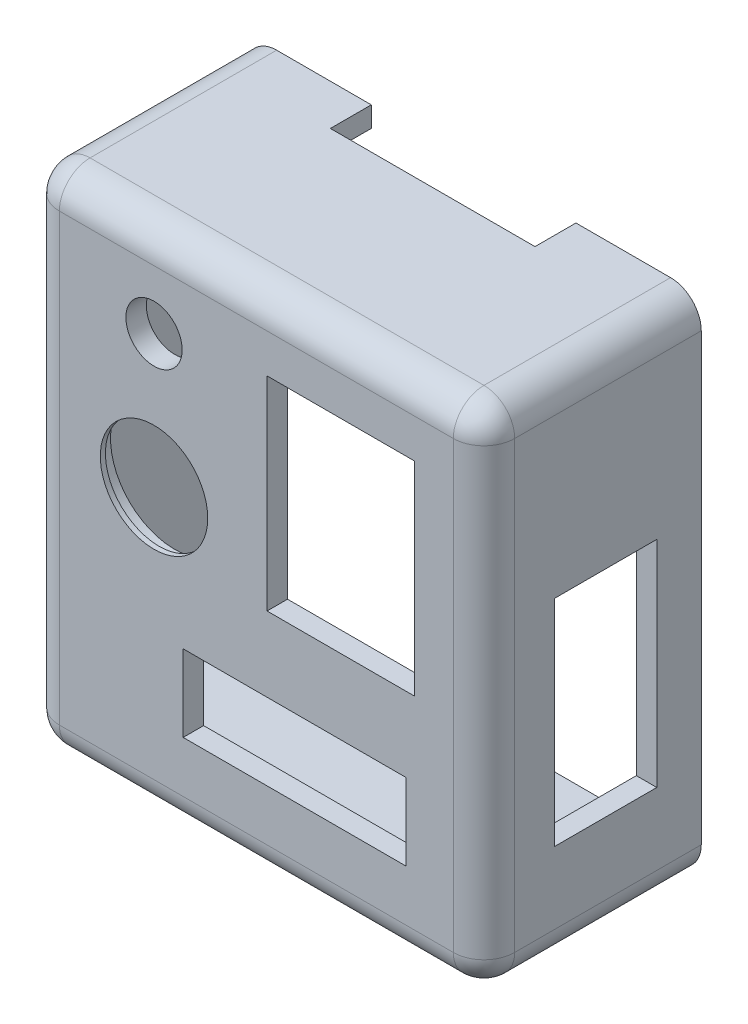
SolidWorks part; units mm, degrees
ref_plane "Front Plane" through (0, 0, 0) normal (0, 0, 1) x (1, 0, 0)
ref_plane "Top Plane" through (0, 0, 0) normal (0, 1, 0) x (1, 0, 0)
ref_plane "Right Plane" through (0, 0, 0) normal (1, 0, 0) x (0, 0, -1)
sketch "Sketch1" plane through (0, 0, 0) normal (0, 0, 1) x (1, 0, 0)
  line L1 (-64.2938, -72.2313) -> (64.2937, -72.2313)
  line L2 (-64.2938, -72.2313) -> (-64.2938, 72.2313)
  line L3 (-64.2938, 72.2313) -> (64.2937, 72.2313)
  line L4 (64.2937, -72.2313) -> (64.2937, 72.2313)
  line L5 (-64.2938, -72.2313) -> (64.2937, 72.2313) construction
  line L6 (-64.2938, 72.2313) -> (64.2937, -72.2313) construction
  point P0 (0, 0)
  dimension "D1" = 128.5875
  dimension "D2" = 144.4625
extrude "Boss-Extrude1" add sketch "Sketch1" against normal blind 61.0718 contours L3 L4 L1 L2
shell "Shell1" thickness 6.35
sketch "Sketch2" plane through (0, 0, 6.35) normal (0, 0, 1) x (1, 0, 0)
  line L0 (-70.6438, 78.5812) -> (70.6437, 78.5812) construction
  line L1 (-70.6438, -78.5812) -> (-70.6438, 78.5812) construction
  line L2 (70.6437, -78.5812) -> (70.6437, 78.5812) construction
  line L3 (3.3337, 56.9912) -> (49.0537, 56.9912)
  line L4 (3.3337, 56.9912) -> (3.3337, -6.1912)
  line L5 (3.3337, -6.1912) -> (49.0537, -6.1912)
  line L6 (49.0537, 56.9912) -> (49.0537, -6.1912)
  line L7 (3.3337, 56.9912) -> (49.0537, -6.1912) construction
  line L8 (3.3337, -6.1912) -> (49.0537, 56.9912) construction
  line L9 (-70.6438, -78.5812) -> (70.6437, -78.5812) construction
  line L10 (-22.7013, -29.3687) -> (46.5137, -29.3687)
  line L11 (-22.7013, -29.3687) -> (-22.7013, -53.1812)
  line L12 (-22.7013, -53.1812) -> (46.5137, -53.1812)
  line L13 (46.5137, -29.3687) -> (46.5137, -53.1812)
  line L14 (-22.7013, -29.3687) -> (46.5137, -53.1812) construction
  line L15 (-22.7013, -53.1812) -> (46.5137, -29.3687) construction
  circle A0 centre (-31.75, 50.8) radius 8.7312
  circle A1 centre (-31.75, 9.525) radius 19.8438
  point P8 (26.1937, 25.4)
  point P15 (11.9062, -41.275)
  dimension "D1" = 17.4625
  dimension "D4" = 39.6875
  dimension "D2" = 27.7812
  dimension "D3" = 38.8937
  dimension "D5" = 38.8937
  dimension "D6" = 69.0563
  dimension "D7" = 45.72
  dimension "D8" = 63.1825
  dimension "D9" = 21.59
  dimension "D10" = 21.59
  dimension "D11" = 69.215
  dimension "D12" = 23.8125
  dimension "D13" = 25.4
  dimension "D14" = 24.13
extrude "Cut-Extrude1" cut sketch "Sketch2" against normal through all
sketch "Sketch3" plane through (70.6437, 0, 0) normal (1, 0, 0) x (0, 0, -1)
  line L1 (15.5219, 19.9072) -> (47.2719, 19.9072)
  line L2 (15.5219, 19.9072) -> (15.5219, -46.7678)
  line L3 (15.5219, -46.7678) -> (47.2719, -46.7678)
  line L4 (47.2719, 19.9072) -> (47.2719, -46.7678)
  line L5 (15.5219, 19.9072) -> (47.2719, -46.7678) construction
  line L6 (15.5219, -46.7678) -> (47.2719, 19.9072) construction
  line L9 (61.0718, 78.5812) -> (-6.35, 78.5812) construction
  line L10 (-6.35, -78.5812) -> (-6.35, 78.5812) construction
  point P0 (31.3969, -13.4302)
  dimension "D1" = 31.75
  dimension "D2" = 66.675
  dimension "D3" = 58.674
  dimension "D4" = 21.8719
extrude "Cut-Extrude2" cut sketch "Sketch3" against normal up to surface (6.35 mm away) up to face at (64.2937, 0, -30.5359)
sketch "Sketch4" plane through (0, 0, 6.35) normal (0, 0, 1) x (1, 0, 0)
  circle A0 centre (-31.75, 9.525) radius 19.8438 construction
  circle A1 centre (-31.75, 9.525) radius 19.8438
  circle A2 centre (-31.75, 9.525) radius 16.6687
  dimension "D1" = 3.175
extrude "Boss-Extrude2" add sketch "Sketch4" against normal blind 1.5875
sketch "Sketch5" plane through (0, 78.5812, 0) normal (0, 1, 0) x (1, 0, 0)
  line L0 (-70.6438, 61.0718) -> (70.6437, 61.0718) construction
  line L1 (-31.75, 61.0718) -> (31.75, 61.0718)
  line L2 (-31.75, 61.0718) -> (-31.75, 48.3718)
  line L3 (-31.75, 48.3718) -> (31.75, 48.3718)
  line L4 (31.75, 61.0718) -> (31.75, 48.3718)
  point P6 (0, 61.0718)
  point P7 (0, 61.0718)
  dimension "D1" = 63.5
  dimension "D2" = 12.7
extrude "Cut-Extrude3" cut sketch "Sketch5" against normal up to surface (6.35 mm away) up to face at (0, 72.2313, -30.5359)
fillet "Fillet1" radius 9.525 8 edges at (70.6437, 78.5812, -27.3609) (-70.6438, 78.5812, -27.3609) (-70.6438, -78.5812, -27.3609) (70.6437, -78.5812, -27.3609) (-70.6438, 0, 6.35) (0, -78.5812, 6.35) (70.6437, 0, 6.35) (0, 78.5812, 6.35)
fillet "Fillet2" radius 3.175 8 edges at (-64.2938, -72.2313, -30.5359) (64.2937, -72.2313, -30.5359) (0, -72.2313, 0) (64.2937, 0, 0) (-64.2938, 0, 0) (-64.2938, 72.2313, -30.5359) (0, 72.2313, 0) (64.2937, 72.2313, -30.5359)
equation "\"diameter1\"= 0.6875in"
equation "\"topcircle1totop\"= 0.5 + 0.25 + ( 0.6875 / 2 )"
equation "\"leftcircle1toleft\"= 0.9375 + 0.25 + ( 0.6875 / 2 )"
equation "\"D1@Sketch2\"=\"diameter1\""
equation "\"D2@Sketch2\"=\"topcircle1totop\""
equation "\"D3@Sketch2\"=\"leftcircle1toleft\""
equation "\"diameter2\"= 1.5625in"
equation "\"topcircle2totop\"= 1.6875in + 0.25 + ( 1.5625 / 2 )"
equation "\"leftcircle2totop\"= 0.5in + 0.25 + ( 1.5625 / 2 )"
equation "\"D4@Sketch2\"=\"diameter2\""
equation "\"D5@Sketch2\"=\"leftcircle2totop\""
equation "\"D6@Sketch2\"=\"topcircle2totop\""
equation "\"boxedgetoside\"= 0.5in + 0.25 + 0.1"
equation "\"topboxtopedge\"= 1.8in"
equation "\"topboxsideedge\"= 2.4875in"
equation "\"bottomboxsideedge\"= 0.9375in"
equation "\"bottomboxtopedge\"= 2.725in"
equation "\"D7@Sketch2\"=\"topboxtopedge\""
equation "\"D8@Sketch2\"=\"topboxsideedge\""
equation "\"D9@Sketch2\"=\"boxedgetoside\""
equation "\"D10@Sketch2\"=\"boxedgetoside\""
equation "\"D11@Sketch2\"=\"bottomboxtopedge\""
equation "\"D12@Sketch2\"=\"bottomboxsideedge\""
equation "\"D13@Sketch2\"=\"bottomboxtobottomedge\""
equation "\"D14@Sketch2\"=\"bottomboxtorightedge\""
equation "\"sideboxtoleftedge\"= 0.5625 + 0.0772 / 2 + 0.26in"
equation "\"sideboxtotopedge\"= 2 + 0.25 + 0.06in"
equation "\"sideboxwidth\"= 1.25in"
equation "\"sideboxheight\"= 2.625in"
equation "\"D1@Sketch3\"=\"sideboxwidth\""
equation "\"D2@Sketch3\"=\"sideboxheight\""
equation "\"D3@Sketch3\"=\"sideboxtotopedge\""
equation "\"D4@Sketch3\"=\"sideboxtoleftedge\""
equation "\"bottomboxtorightedge\"= 0.75 + 0.2in"
equation "\"bottomboxtobottomedge\"= 0.75 + 0.25in"
